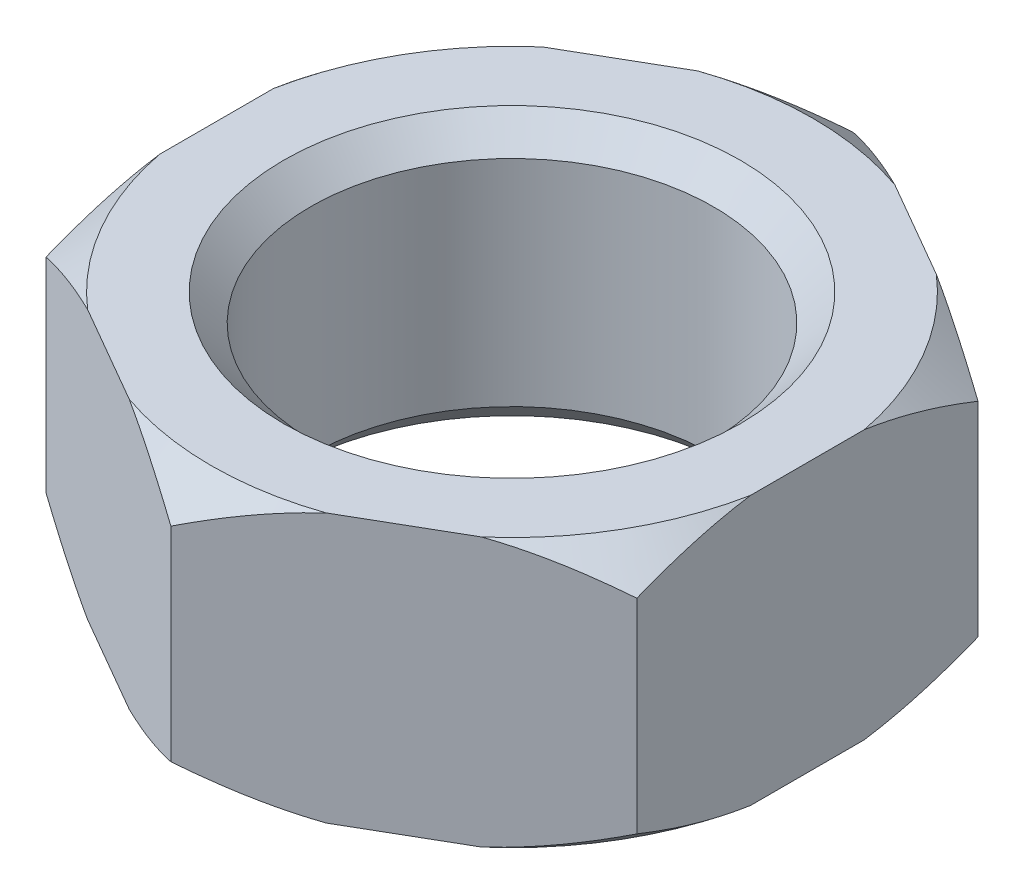
SolidWorks part; units mm, degrees
ref_plane "Front" through (0, 0, 0) normal (0, 0, 1) x (1, 0, 0)
ref_plane "Top" through (0, 0, 0) normal (0, 1, 0) x (1, 0, 0)
ref_plane "Right" through (0, 0, 0) normal (1, 0, 0) x (0, 0, -1)
sketch "Sketch1" plane through (0, 0, 0) normal (0, 1, 0) x (1, 0, 0)
  line L1 (0, 12.7017) -> (-11, 6.3509)
  line L2 (-11, 6.3509) -> (-11, -6.3509)
  line L3 (-11, -6.3509) -> (0, -12.7017)
  line L4 (0, -12.7017) -> (11, -6.3509)
  line L5 (11, -6.3509) -> (11, 6.3509)
  line L6 (11, 6.3509) -> (0, 12.7017)
  circle A0 centre (0, 0) radius 11 construction
  dimension "D1" = 22
extrude "Boss-Extrude1" add sketch "Sketch1" along normal blind 10
sketch "Sketch2" plane through (0, 10, 0) normal (0, 1, 0) x (1, 0, 0)
  circle A0 centre (0, 0) radius 7.5
  dimension "D1" = 15
extrude "Cut-Extrude1" cut sketch "Sketch2" against normal through all
cosmetic thread "Cosmetic Thread1" parameters "D1"=5, "D2"=24
chamfer "Chamfer1" distance 1 angle 45 2 edges at (0, 10, 7.5) (0, 0, 7.5)
sketch "Sketch3" plane through (0, 0, 0) normal (1, 0, 0) x (0, 0, -1)
  line L0 (0, 0) -> (0, 12.4722) construction
  line L1 (-12.7017, 10) -> (-11.2017, 10)
  line L2 (-12.7017, 10) -> (-6.3509, 10) construction
  line L3 (-11.2017, 10) -> (-12.7017, 8.8)
  line L4 (-12.7017, 10) -> (-12.7017, 0) construction
  line L5 (-12.7017, 8.8) -> (-12.7017, 10)
  line L6 (-12.7017, 5) -> (12.7017, 5) construction
  line L7 (12.7017, 10) -> (12.7017, 0) construction
  line L8 (-12.7017, 1.2) -> (-12.7017, 0)
  line L9 (-11.2017, 0) -> (-12.7017, 1.2)
  line L10 (-12.7017, 0) -> (-11.2017, 0)
  dimension "D1" = 1.5
  dimension "D2" = 1.2
revolve "Cut-Revolve1" cut sketch "Sketch3" angle 360 about L0
